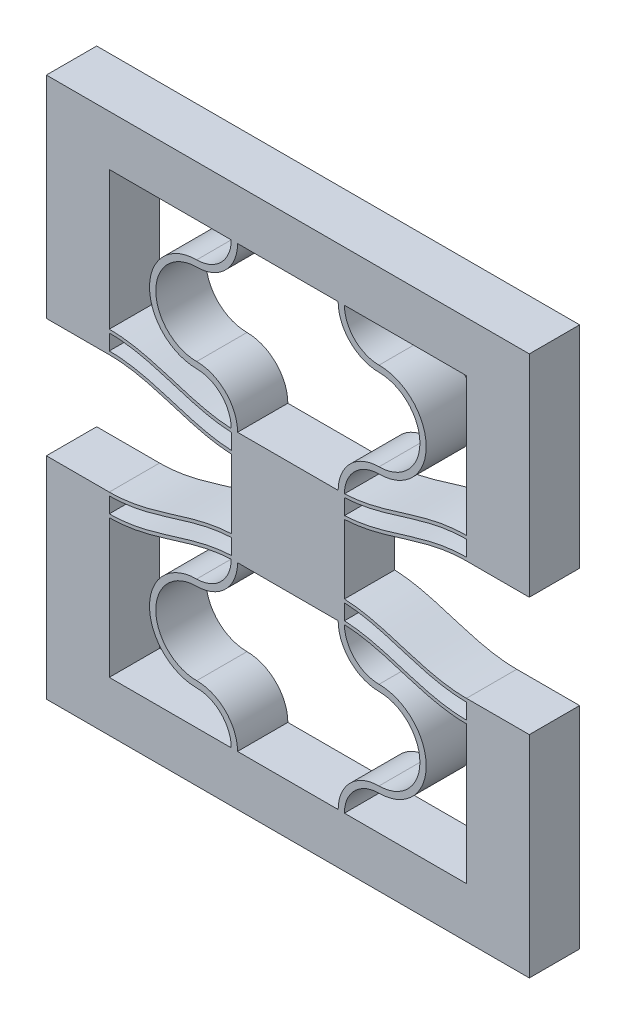
SolidWorks part; units mm, degrees
ref_plane "Front Plane" through (0, 0, 0) normal (0, 0, 1) x (1, 0, 0)
ref_plane "Top Plane" through (0, 0, 0) normal (0, 1, 0) x (1, 0, 0)
ref_plane "Right Plane" through (0, 0, 0) normal (1, 0, 0) x (0, 0, -1)
sketch "Sketch1" plane through (0, 0, 0) normal (0, 0, 1) x (1, 0, 0)
  line L4 (0, 11) -> (0, 0)
  line L5 (10.2, 0) -> (10.2, 13) construction
  line L6 (10.2, 13) -> (10.2, 15.9882) construction
  line L17 (9.7, 0) -> (0, 0)
  line L18 (10.7, 0) -> (20.4, 0)
  line L19 (20.4, 0) -> (20.4, 11)
  line L20 (10.7, 13.2482) -> (10.7, 14.4882)
  line L21 (9.7, 13.2482) -> (9.7, 14.4882)
  line L22 (10.7, 14.7482) -> (10.7, 15.9882)
  line L23 (10.7, 15.9882) -> (9.7, 15.9882)
  line L24 (9.7, 15.9882) -> (9.7, 14.7482)
  line L31 (-5, 12.76) -> (-5, -4)
  line L32 (-5, -4) -> (25.4, -4)
  line L33 (25.4, -4) -> (25.4, 12.76)
  line L34 (0, 11.26) -> (0, 12.5)
  line L36 (-5, 12.76) -> (0, 12.76)
  line L37 (25.4, 12.76) -> (20.4, 12.76)
  line L38 (20.4, 11.26) -> (20.4, 12.5)
  arc A0 (10.2, 13) -> (6.95, 9.75) centre (6.95, 13) cw
  arc A1 (6.95, 9.75) -> (6.95, 3.25) centre (6.95, 6.5) ccw
  arc A2 (6.95, 3.25) -> (10.2, 0) centre (6.95, 0) cw
  arc A3 (9.7, 12.9882) -> (6.95, 10.25) centre (6.95, 13) cw
  arc A4 (6.95, 10.25) -> (6.95, 2.75) centre (6.95, 6.5) ccw
  arc A5 (6.95, 2.75) -> (9.7, 0) centre (6.95, 0) cw
  arc A6 (9.7, 13) -> (6.95, 10.25) centre (6.95, 13) cw construction
  arc A7 (13.45, 3.25) -> (10.2, 0) centre (13.45, 0) ccw
  arc A8 (13.45, 2.75) -> (10.7, 0) centre (13.45, 0) ccw
  arc A9 (13.45, 9.75) -> (13.45, 3.25) centre (13.45, 6.5) cw
  arc A10 (13.45, 10.25) -> (13.45, 2.75) centre (13.45, 6.5) cw
  arc A11 (10.7, 12.9882) -> (13.45, 10.25) centre (13.45, 13) ccw
  arc A12 (10.2, 13) -> (13.45, 9.75) centre (13.45, 13) ccw
  spline S0 degree 4 poles (-2.04, 11.451) (-1.9765, 11.4395) (-1.8495, 11.4173) (-1.6581, 11.3865) (-1.4034, 11.3507) (-1.1461, 11.3206) (-0.8947, 11.2963) (-0.6305, 11.2779) (-0.3994, 11.2656) (-0.0407, 11.2587) (0.1118, 11.2598) (0.4714, 11.2679) (0.718, 11.2841) (1.0341, 11.3073) (1.3605, 11.3444) (1.7553, 11.3997) (2.2012, 11.4781) (2.7158, 11.5853) (3.221, 11.71) (3.7265, 11.8477) (4.1644, 11.9751) (4.5393, 12.0877) (5.1935, 12.2883) (6.0661, 12.5594) (7.0383, 12.8395) (8.1229, 13.0766) (9.0278, 13.2068) (9.8085, 13.2648) (10.5915, 13.2648) (11.3722, 13.2068) (12.2771, 13.0765) (13.1705, 12.8813) (14.052, 12.6406) (14.8329, 12.4044) (15.3934, 12.231) (15.8608, 12.0877) (16.2353, 11.9751) (16.6741, 11.8477) (17.0991, 11.7315) (17.5115, 11.6281) (17.9254, 11.535) (18.2782, 11.4641) (18.6464, 11.3997) (19.0359, 11.3444) (19.4206, 11.302) (19.77, 11.2769) (20.0462, 11.2642) (20.3512, 11.2594) (20.494, 11.2598) (20.8071, 11.2656) (21.0258, 11.2779) (21.2971, 11.2963) (21.5449, 11.3206) (21.804, 11.3507) (22.0578, 11.3865) (22.2496, 11.4173) (22.3766, 11.4395) (22.4399, 11.451) knots 0 0 0 0 0 0.01033 0.02066 0.030989 0.041319 0.051524 0.061728 0.071933 0.082137 0.097795 0.105623 0.113452 0.129109 0.144767 0.160424 0.176081 0.20226 0.228439 0.244097 0.259754 0.275411 0.291069 0.353698 0.406056 0.437371 0.468685 0.5 0.531315 0.562629 0.593944 0.646302 0.677617 0.708931 0.724589 0.740246 0.755903 0.771561 0.79774 0.810829 0.823919 0.839576 0.855233 0.870891 0.886548 0.902205 0.910034 0.917863 0.928067 0.938272 0.948476 0.958681 0.969011 0.97934 0.98967 1 1 1 1 1 construction
  spline S1 degree 4 poles (0, 11.26) (0.0817, 11.26) (0.2002, 11.2618) (0.4714, 11.2679) (0.718, 11.2841) (1.0341, 11.3073) (1.3605, 11.3444) (1.7553, 11.3997) (2.2012, 11.4781) (2.7158, 11.5853) (3.221, 11.71) (3.7265, 11.8477) (4.1644, 11.9751) (4.5393, 12.0877) (5.1935, 12.2883) (6.0661, 12.5594) (7.0383, 12.8395) (8.1229, 13.0766) (9.0278, 13.2068) (9.8085, 13.2648) (10.5915, 13.2648) (11.3722, 13.2068) (12.2771, 13.0765) (13.1705, 12.8813) (14.052, 12.6406) (14.8329, 12.4044) (15.3934, 12.231) (15.8608, 12.0877) (16.2353, 11.9751) (16.6741, 11.8477) (17.0991, 11.7315) (17.5115, 11.6281) (17.9254, 11.535) (18.2782, 11.4641) (18.6464, 11.3997) (19.0359, 11.3444) (19.4206, 11.302) (19.77, 11.2769) (20.0462, 11.2642) (20.2762, 11.2606) (20.3591, 11.26) (20.4, 11.26) knots 0.082137 0.082137 0.082137 0.082137 0.082137 0.097795 0.105623 0.113452 0.129109 0.144767 0.160424 0.176081 0.20226 0.228439 0.244097 0.259754 0.275411 0.291069 0.353698 0.406056 0.437371 0.468685 0.5 0.531315 0.562629 0.593944 0.646302 0.677617 0.708931 0.724589 0.740246 0.755903 0.771561 0.79774 0.810829 0.823919 0.839576 0.855233 0.870891 0.886548 0.902205 0.910034 0.917863 0.917863 0.917863 0.917863 0.917863
  spline S2 degree 4 poles (-2.04, 12.691) (-1.9765, 12.6795) (-1.8495, 12.6573) (-1.6581, 12.6265) (-1.4034, 12.5907) (-1.1461, 12.5606) (-0.8947, 12.5363) (-0.6305, 12.5179) (-0.3994, 12.5056) (-0.0407, 12.4987) (0.1118, 12.4998) (0.4714, 12.5079) (0.718, 12.5241) (1.0341, 12.5473) (1.3605, 12.5844) (1.7553, 12.6397) (2.2012, 12.7181) (2.7158, 12.8253) (3.221, 12.95) (3.7265, 13.0877) (4.1644, 13.2151) (4.5393, 13.3277) (5.1935, 13.5283) (6.0661, 13.7994) (7.0383, 14.0795) (8.1229, 14.3166) (9.0278, 14.4468) (9.8085, 14.5048) (10.5915, 14.5048) (11.3722, 14.4468) (12.2771, 14.3165) (13.1705, 14.1213) (14.052, 13.8806) (14.8329, 13.6444) (15.3934, 13.471) (15.8608, 13.3277) (16.2353, 13.2151) (16.6741, 13.0877) (17.0991, 12.9715) (17.5115, 12.8681) (17.9254, 12.775) (18.2782, 12.7041) (18.6464, 12.6397) (19.0359, 12.5844) (19.4206, 12.542) (19.77, 12.5169) (20.0462, 12.5042) (20.3512, 12.4994) (20.494, 12.4998) (20.8071, 12.5056) (21.0258, 12.5179) (21.2971, 12.5363) (21.5449, 12.5606) (21.804, 12.5907) (22.0578, 12.6265) (22.2496, 12.6573) (22.3766, 12.6795) (22.4399, 12.691) knots 0 0 0 0 0 0.01033 0.02066 0.030989 0.041319 0.051524 0.061728 0.071933 0.082137 0.097795 0.105623 0.113452 0.129109 0.144767 0.160424 0.176081 0.20226 0.228439 0.244097 0.259754 0.275411 0.291069 0.353698 0.406056 0.437371 0.468685 0.5 0.531315 0.562629 0.593944 0.646302 0.677617 0.708931 0.724589 0.740246 0.755903 0.771561 0.79774 0.810829 0.823919 0.839576 0.855233 0.870891 0.886548 0.902205 0.910034 0.917863 0.928067 0.938272 0.948476 0.958681 0.969011 0.97934 0.98967 1 1 1 1 1 construction
  spline S3 degree 4 poles (0, 12.5) (0.0817, 12.5) (0.2002, 12.5018) (0.4714, 12.5079) (0.718, 12.5241) (1.0341, 12.5473) (1.3605, 12.5844) (1.7553, 12.6397) (2.2012, 12.7181) (2.7158, 12.8253) (3.221, 12.95) (3.7265, 13.0877) (4.1644, 13.2151) (4.5393, 13.3277) (5.1935, 13.5283) (6.0661, 13.7994) (7.0383, 14.0795) (8.1229, 14.3166) (9.0278, 14.4468) (9.8085, 14.5048) (10.5915, 14.5048) (11.3722, 14.4468) (12.2771, 14.3165) (13.1705, 14.1213) (14.052, 13.8806) (14.8329, 13.6444) (15.3934, 13.471) (15.8608, 13.3277) (16.2353, 13.2151) (16.6741, 13.0877) (17.0991, 12.9715) (17.5115, 12.8681) (17.9254, 12.775) (18.2782, 12.7041) (18.6464, 12.6397) (19.0359, 12.5844) (19.4206, 12.542) (19.77, 12.5169) (20.0462, 12.5042) (20.2762, 12.5006) (20.3591, 12.5) (20.4, 12.5) knots 0.082137 0.082137 0.082137 0.082137 0.082137 0.097795 0.105623 0.113452 0.129109 0.144767 0.160424 0.176081 0.20226 0.228439 0.244097 0.259754 0.275411 0.291069 0.353698 0.406056 0.437371 0.468685 0.5 0.531315 0.562629 0.593944 0.646302 0.677617 0.708931 0.724589 0.740246 0.755903 0.771561 0.79774 0.810829 0.823919 0.839576 0.855233 0.870891 0.886548 0.902205 0.910034 0.917863 0.917863 0.917863 0.917863 0.917863
  spline S4 degree 4 poles (-2.04, 12.951) (-1.9765, 12.9395) (-1.8495, 12.9173) (-1.6581, 12.8865) (-1.4034, 12.8507) (-1.1461, 12.8206) (-0.8947, 12.7963) (-0.6305, 12.7779) (-0.3994, 12.7656) (-0.0407, 12.7587) (0.1118, 12.7598) (0.4714, 12.7679) (0.718, 12.7841) (1.0341, 12.8073) (1.3605, 12.8444) (1.7553, 12.8997) (2.2012, 12.9781) (2.7158, 13.0853) (3.221, 13.21) (3.7265, 13.3477) (4.1644, 13.4751) (4.5393, 13.5877) (5.1935, 13.7883) (6.0661, 14.0594) (7.0383, 14.3395) (8.1229, 14.5766) (9.0278, 14.7068) (9.8085, 14.7648) (10.5915, 14.7648) (11.3722, 14.7068) (12.2771, 14.5765) (13.1705, 14.3813) (14.052, 14.1406) (14.8329, 13.9044) (15.3934, 13.731) (15.8608, 13.5877) (16.2353, 13.4751) (16.6741, 13.3477) (17.0991, 13.2315) (17.5115, 13.1281) (17.9254, 13.035) (18.2782, 12.9641) (18.6464, 12.8997) (19.0359, 12.8444) (19.4206, 12.802) (19.77, 12.7769) (20.0462, 12.7642) (20.3512, 12.7594) (20.494, 12.7598) (20.8071, 12.7656) (21.0258, 12.7779) (21.2971, 12.7963) (21.5449, 12.8206) (21.804, 12.8507) (22.0578, 12.8865) (22.2496, 12.9173) (22.3766, 12.9395) (22.4399, 12.951) knots 0 0 0 0 0 0.01033 0.02066 0.030989 0.041319 0.051524 0.061728 0.071933 0.082137 0.097795 0.105623 0.113452 0.129109 0.144767 0.160424 0.176081 0.20226 0.228439 0.244097 0.259754 0.275411 0.291069 0.353698 0.406056 0.437371 0.468685 0.5 0.531315 0.562629 0.593944 0.646302 0.677617 0.708931 0.724589 0.740246 0.755903 0.771561 0.79774 0.810829 0.823919 0.839576 0.855233 0.870891 0.886548 0.902205 0.910034 0.917863 0.928067 0.938272 0.948476 0.958681 0.969011 0.97934 0.98967 1 1 1 1 1 construction
  spline S5 degree 4 poles (0, 12.76) (0.0817, 12.76) (0.2002, 12.7618) (0.4714, 12.7679) (0.718, 12.7841) (1.0341, 12.8073) (1.3605, 12.8444) (1.7553, 12.8997) (2.2012, 12.9781) (2.7158, 13.0853) (3.221, 13.21) (3.7265, 13.3477) (4.1644, 13.4751) (4.5393, 13.5877) (5.1935, 13.7883) (6.0661, 14.0594) (7.0383, 14.3395) (8.1229, 14.5766) (9.0278, 14.7068) (9.8085, 14.7648) (10.5915, 14.7648) (11.3722, 14.7068) (12.2771, 14.5765) (13.1705, 14.3813) (14.052, 14.1406) (14.8329, 13.9044) (15.3934, 13.731) (15.8608, 13.5877) (16.2353, 13.4751) (16.6741, 13.3477) (17.0991, 13.2315) (17.5115, 13.1281) (17.9254, 13.035) (18.2782, 12.9641) (18.6464, 12.8997) (19.0359, 12.8444) (19.4206, 12.802) (19.77, 12.7769) (20.0462, 12.7642) (20.2762, 12.7606) (20.3591, 12.76) (20.4, 12.76) knots 0.082137 0.082137 0.082137 0.082137 0.082137 0.097795 0.105623 0.113452 0.129109 0.144767 0.160424 0.176081 0.20226 0.228439 0.244097 0.259754 0.275411 0.291069 0.353698 0.406056 0.437371 0.468685 0.5 0.531315 0.562629 0.593944 0.646302 0.677617 0.708931 0.724589 0.740246 0.755903 0.771561 0.79774 0.810829 0.823919 0.839576 0.855233 0.870891 0.886548 0.902205 0.910034 0.917863 0.917863 0.917863 0.917863 0.917863
  spline S8 degree 4 poles (-2.04, 11.191) (-1.9765, 11.1795) (-1.8495, 11.1573) (-1.6581, 11.1265) (-1.4034, 11.0907) (-1.1461, 11.0606) (-0.8947, 11.0363) (-0.6305, 11.0179) (-0.3994, 11.0056) (-0.0407, 10.9987) (0.1118, 10.9998) (0.4714, 11.0079) (0.718, 11.0241) (1.0341, 11.0473) (1.3605, 11.0844) (1.7553, 11.1397) (2.2012, 11.2181) (2.7158, 11.3253) (3.221, 11.45) (3.7265, 11.5877) (4.1644, 11.7151) (4.5393, 11.8277) (5.1935, 12.0283) (6.0661, 12.2994) (7.0383, 12.5795) (8.1229, 12.8166) (9.0278, 12.9468) (9.8085, 13.0048) (10.5915, 13.0048) (11.3722, 12.9468) (12.2771, 12.8165) (13.1705, 12.6213) (14.052, 12.3806) (14.8329, 12.1444) (15.3934, 11.971) (15.8608, 11.8277) (16.2353, 11.7151) (16.6741, 11.5877) (17.0991, 11.4715) (17.5115, 11.3681) (17.9254, 11.275) (18.2782, 11.2041) (18.6464, 11.1397) (19.0359, 11.0844) (19.4206, 11.042) (19.77, 11.0169) (20.0462, 11.0042) (20.3512, 10.9994) (20.494, 10.9998) (20.8071, 11.0056) (21.0258, 11.0179) (21.2971, 11.0363) (21.5449, 11.0606) (21.804, 11.0907) (22.0578, 11.1265) (22.2496, 11.1573) (22.3766, 11.1795) (22.4399, 11.191) knots 0 0 0 0 0 0.01033 0.02066 0.030989 0.041319 0.051524 0.061728 0.071933 0.082137 0.097795 0.105623 0.113452 0.129109 0.144767 0.160424 0.176081 0.20226 0.228439 0.244097 0.259754 0.275411 0.291069 0.353698 0.406056 0.437371 0.468685 0.5 0.531315 0.562629 0.593944 0.646302 0.677617 0.708931 0.724589 0.740246 0.755903 0.771561 0.79774 0.810829 0.823919 0.839576 0.855233 0.870891 0.886548 0.902205 0.910034 0.917863 0.928067 0.938272 0.948476 0.958681 0.969011 0.97934 0.98967 1 1 1 1 1 construction
  spline S9 degree 4 poles (0, 11) (0.0817, 11) (0.2002, 11.0018) (0.4714, 11.0079) (0.718, 11.0241) (1.0341, 11.0473) (1.3605, 11.0844) (1.7553, 11.1397) (2.2012, 11.2181) (2.7158, 11.3253) (3.221, 11.45) (3.7265, 11.5877) (4.1644, 11.7151) (4.5393, 11.8277) (5.1935, 12.0283) (6.0661, 12.2994) (7.0383, 12.5795) (8.1229, 12.8166) (9.0278, 12.9468) (9.8085, 13.0048) (10.5915, 13.0048) (11.3722, 12.9468) (12.2771, 12.8165) (13.1705, 12.6213) (14.052, 12.3806) (14.8329, 12.1444) (15.3934, 11.971) (15.8608, 11.8277) (16.2353, 11.7151) (16.6741, 11.5877) (17.0991, 11.4715) (17.5115, 11.3681) (17.9254, 11.275) (18.2782, 11.2041) (18.6464, 11.1397) (19.0359, 11.0844) (19.4206, 11.042) (19.77, 11.0169) (20.0462, 11.0042) (20.2762, 11.0006) (20.3591, 11) (20.4, 11) knots 0.082137 0.082137 0.082137 0.082137 0.082137 0.097795 0.105623 0.113452 0.129109 0.144767 0.160424 0.176081 0.20226 0.228439 0.244097 0.259754 0.275411 0.291069 0.353698 0.406056 0.437371 0.468685 0.5 0.531315 0.562629 0.593944 0.646302 0.677617 0.708931 0.724589 0.740246 0.755903 0.771561 0.79774 0.810829 0.823919 0.839576 0.855233 0.870891 0.886548 0.902205 0.910034 0.917863 0.917863 0.917863 0.917863 0.917863
  dimension "D4" = 0.26
  dimension "D6" = 4
  dimension "D1" = 13
  dimension "D2" = 0.5
  dimension "D3" = 0.26
  dimension "D7" = 5
  dimension "D5" = 1.5
extrude "Boss-Extrude1" add sketch "Sketch1" along normal blind 4
sketch "Sketch4" plane through (0, 15.9882, 0) normal (0, 1, 0) x (1, 0, 0)
  line L24 (10.7, 0) -> (9.7, 0)
  line L25 (9.7, 0) -> (9.7, -4)
  line L26 (10.7, 0) -> (9.7, 0)
  line L27 (10.7, -4) -> (10.7, 0)
  line L29 (9.7, 0) -> (9.7, -4)
  line L31 (10.7, -4) -> (10.7, 0)
  line L32 (9.7, -4) -> (10.7, -4)
  line L33 (9.7, -4) -> (10.7, -4)
  dimension "D1" = 0
extrude "Boss-Extrude2" add sketch "Sketch4" along normal blind 1.5
mirror "Mirror3" about plane through (0, 17.4882, 0) normal (0, 1, 0) of bodies 179
ref_plane "Plane1" through (10.2, 0, 0) normal (-1, 0, 0) x (0, 0, 1)
split "Split2" trim tools "Plane1" bodies to split 247 102 resulting bodies 225
sketch "Sketch7" plane through (10.2, 0, 0) normal (-1, 0, 0) x (0, 0, 1)
  line L4 (4, 34.9763) -> (4, 38.9763)
  line L12 (0, 13) -> (4, 13)
  line L13 (0, 13) -> (4, 13)
  line L14 (4, 13) -> (4, 21.9763)
  line L15 (4, 13) -> (4, 21.9763)
  line L20 (4, 0) -> (0, 0)
  line L22 (4, 0) -> (0, 0)
  line L23 (0, -4) -> (4, -4)
  line L27 (0, -4) -> (4, -4)
  line L31 (4, 21.9763) -> (0, 21.9763)
  line L32 (4, 21.9763) -> (0, 21.9763)
  line L33 (0, 21.9763) -> (0, 13)
  line L34 (0, 21.9763) -> (0, 13)
  line L36 (4, -4) -> (4, 0)
  line L38 (4, 34.9763) -> (4, 38.9763)
  line L39 (4, 34.9763) -> (4, 38.9763)
  line L40 (4, 38.9763) -> (0, 38.9763)
  line L41 (4, 38.9763) -> (0, 38.9763)
  line L46 (4, 34.9763) -> (4, 38.9763)
  line L51 (0, 38.9763) -> (0, 34.9763)
  line L52 (0, 38.9763) -> (0, 34.9763)
  line L53 (0, 34.9763) -> (4, 34.9763)
  line L54 (0, 34.9763) -> (4, 34.9763)
  line L55 (4, 38.9763) -> (0, 38.9763)
  line L57 (4, 38.9763) -> (0, 38.9763)
  line L59 (4, -4) -> (4, 0)
  line L60 (0, 0) -> (0, -4)
  line L61 (0, 0) -> (0, -4)
  line L62 (0, 38.9763) -> (0, 34.9763)
  line L63 (0, 38.9763) -> (0, 34.9763)
  line L64 (0, 34.9763) -> (4, 34.9763)
  line L65 (0, 34.9763) -> (4, 34.9763)
  dimension "D1" = 0
  dimension "D2" = 0
  dimension "D3" = 0
  dimension "D4" = 0
extrude "Boss-Extrude3" add sketch "Sketch7" along normal blind 4
mirror "Mirror2" about plane through (6.2, 0, 0) normal (-1, 0, 0) of bodies 226
